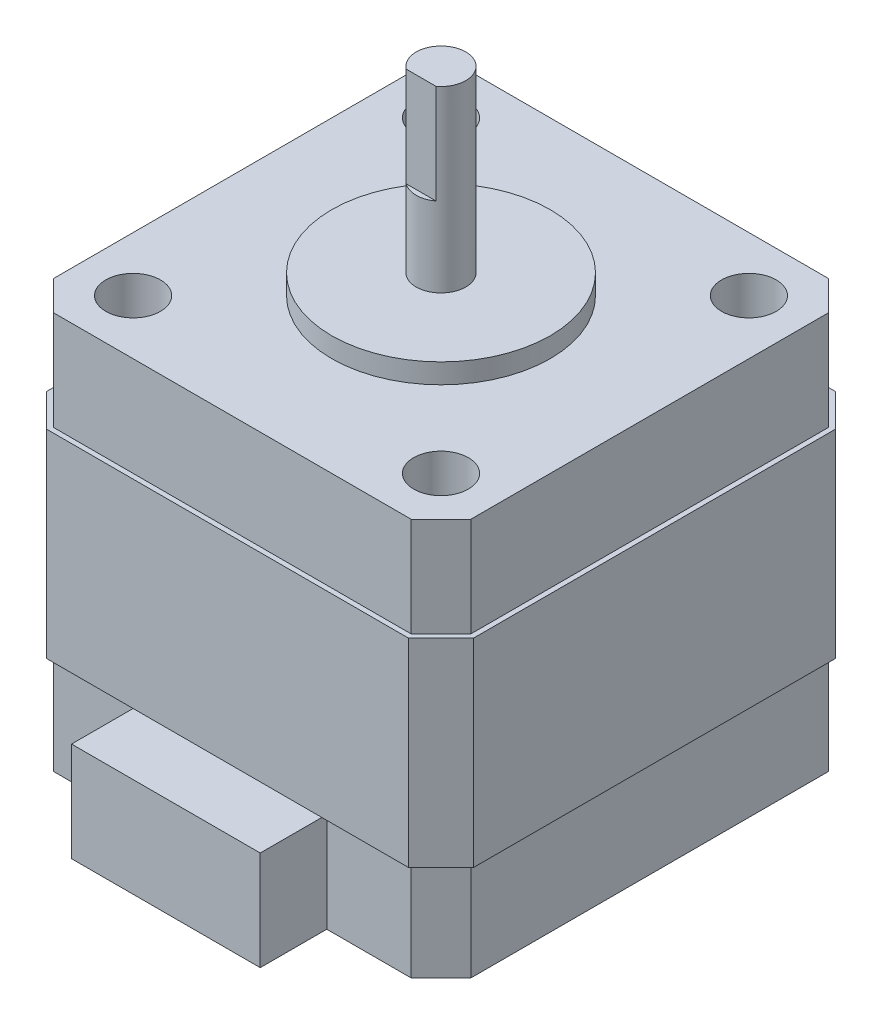
SolidWorks part; units mm, degrees
ref_plane "前视基准面" through (0, 0, 0) normal (0, 0, 1) x (1, 0, 0)
ref_plane "上视基准面" through (0, 0, 0) normal (0, 1, 0) x (1, 0, 0)
ref_plane "右视基准面" through (0, 0, 0) normal (1, 0, 0) x (0, 0, -1)
sketch "草图1" plane through (0, 0, 0) normal (0, 1, 0) x (1, 0, 0)
  line L0 (-21, 18) -> (-18, 21)
  line L1 (-18, 21) -> (18, 21)
  line L2 (-21, 18) -> (-21, -18)
  line L3 (-18, -21) -> (18, -21)
  line L4 (21, 18) -> (21, -18)
  line L5 (-21, 21) -> (21, -21) construction
  line L6 (-21, -21) -> (21, 21) construction
  line L7 (18, 21) -> (21, 18)
  line L8 (18, -21) -> (21, -18)
  line L9 (-21, -18) -> (-18, -21)
  point P0 (0, 0)
  dimension "D1" = 42
  dimension "D2" = 42
extrude "凸台-拉伸1" add sketch "草图1" along normal blind 10
sketch "草图2" plane through (0, 10, 0) normal (0, 1, 0) x (1, 0, 0)
  line L44 (21.5, 18.2071) -> (18.2071, 21.5)
  line L45 (21.5, -18.2071) -> (21.5, 18.2071)
  line L46 (18.2071, -21.5) -> (21.5, -18.2071)
  line L47 (-18.2071, -21.5) -> (18.2071, -21.5)
  line L48 (-21.5, -18.2071) -> (-18.2071, -21.5)
  line L49 (-21.5, 18.2071) -> (-21.5, -18.2071)
  line L50 (-18.2071, 21.5) -> (-21.5, 18.2071)
  line L51 (18.2071, 21.5) -> (-18.2071, 21.5)
  line L52 (21.5, 18.2071) -> (18.2071, 21.5)
  line L53 (21.5, -18.2071) -> (21.5, 18.2071)
  line L54 (18.2071, -21.5) -> (21.5, -18.2071)
  line L55 (-18.2071, -21.5) -> (18.2071, -21.5)
  line L56 (-21.5, -18.2071) -> (-18.2071, -21.5)
  line L57 (-21.5, 18.2071) -> (-21.5, -18.2071)
  line L58 (-18.2071, 21.5) -> (-21.5, 18.2071)
  line L59 (18.2071, 21.5) -> (-18.2071, 21.5)
  dimension "D1" = 0.5
extrude "凸台-拉伸3" add sketch "草图2" along normal blind 20
sketch "草图3" plane through (0, 30, 0) normal (0, 1, 0) x (1, 0, 0)
  line L16 (21, -18) -> (21, 18)
  line L17 (21, 18) -> (18, 21)
  line L18 (18, 21) -> (-18, 21)
  line L19 (-18, 21) -> (-21, 18)
  line L20 (-21, 18) -> (-21, -18)
  line L21 (-21, -18) -> (-18, -21)
  line L22 (-18, -21) -> (18, -21)
  line L23 (18, -21) -> (21, -18)
  line L24 (21, -18) -> (21, 18)
  line L25 (21, 18) -> (18, 21)
  line L26 (18, 21) -> (-18, 21)
  line L27 (-18, 21) -> (-21, 18)
  line L28 (-21, 18) -> (-21, -18)
  line L29 (-21, -18) -> (-18, -21)
  line L30 (-18, -21) -> (18, -21)
  line L31 (18, -21) -> (21, -18)
  dimension "D1" = 0.5
extrude "凸台-拉伸4" add sketch "草图3" along normal blind 10
sketch "草图4" plane through (0, 40, 0) normal (0, 1, 0) x (1, 0, 0)
  circle A0 centre (0, 0) radius 11
  dimension "D1" = 22
extrude "凸台-拉伸5" add sketch "草图4" along normal blind 2
sketch "草图5" plane through (0, 42, 0) normal (0, 1, 0) x (1, 0, 0)
  circle A0 centre (0, 0) radius 2.5
  dimension "D1" = 5
extrude "凸台-拉伸6" add sketch "草图5" along normal blind 18
sketch "草图6" plane through (0, 0, 21) normal (0, 0, 1) x (1, 0, 0)
  line L0 (-9.5, 0) -> (9.5, 0)
  line L1 (-9.5, 10) -> (9.5, 10)
  line L2 (-9.5, 10) -> (-9.5, 0)
  line L4 (9.5, 10) -> (9.5, 0)
  line L5 (-9.5, 10) -> (0, 0) construction
  line L6 (0, 0) -> (9.5, 10) construction
  point P0 (0, 0)
extrude "凸台-拉伸7" add sketch "草图6" along normal blind 6.7
sketch "草图7" plane through (0, 60, 0) normal (0, 1, 0) x (1, 0, 0)
  line L0 (-1.5, -2) -> (1.5, -2)
  arc A0 (-1.5, -2) -> (1.5, -2) centre (0, 0) ccw
  dimension "D1" = 2
  dimension "D2" = 5
extrude "切除-拉伸1" cut sketch "草图7" against normal blind 10
hole_wizard "M3 六角头机械螺钉的柱形沉头孔1" positions "草图9" profile "草图8" counterbore size "M3" standard "ANSI Metric"
sketch "草图9" plane through (0, 40, 0) normal (0, 1, 0) x (1, 0, 0)
  line L0 (0, 21) -> (0, -21) construction
  line L1 (18, 21) -> (-18, 21) construction
  line L2 (-18, -21) -> (18, -21) construction
  point P0 (-15.5, 15.5)
  point P2 (15.5, 15.5)
  point P4 (-15.5, -15.5)
  point P6 (15.5, -15.5)
  dimension "D1" = 31
  dimension "D2" = 31
  dimension "D3" = 15.5
  dimension "D4" = 31
sketch "草图8" plane through (-15.5, 40, -15.5) normal (1, 0, 0) x (0, 0, 1)
  line L0 (0, 0) -> (0, 14.7511)
  line L1 (0, 14.7511) -> (1.25, 14)
  line L2 (1.25, 14) -> (1.25, 4.5)
  line L3 (1.25, 4.5) -> (2.75, 4.5)
  line L4 (2.75, 4.5) -> (2.75, 0)
  line L5 (2.75, 0) -> (0, 0)
  line L10 (0, 14.7511) -> (-1.25, 14) construction
  line L11 (0, -6.35) -> (0, 107.95) construction
  dimension "孔直径" = 2.5
  dimension "孔深度" = 14
  dimension "柱形沉头孔直径" = 5.5
  dimension "柱形沉头孔深度" = 4.5
  dimension "导头角度" = 118
